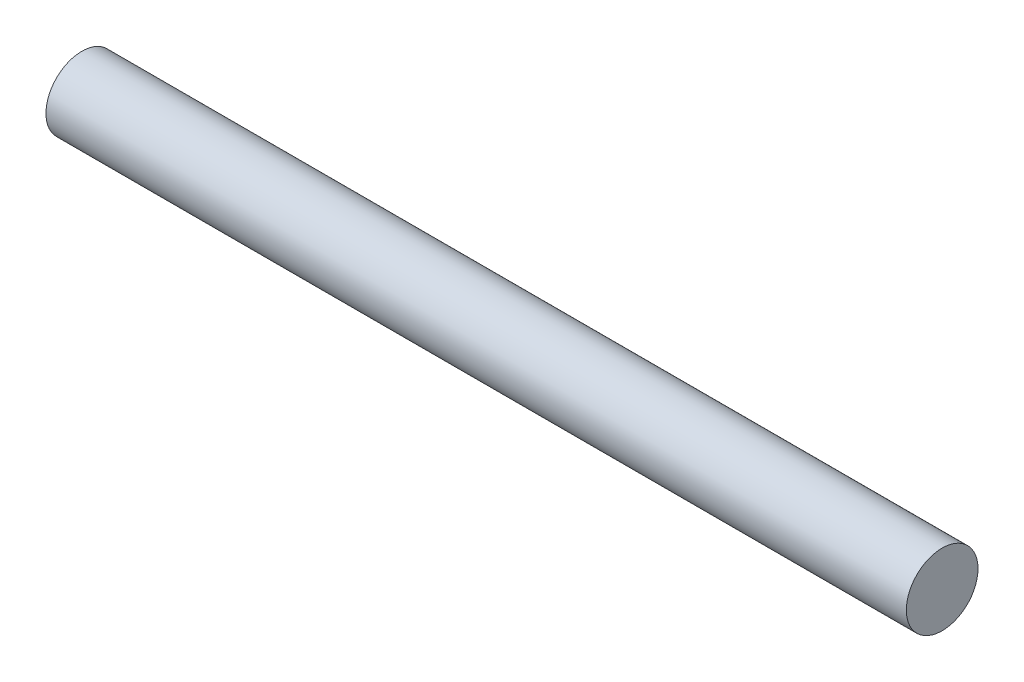
SolidWorks part; units mm, degrees
ref_plane "Front Plane" through (0, 0, 0) normal (0, 0, 1) x (1, 0, 0)
ref_plane "Top Plane" through (0, 0, 0) normal (0, 1, 0) x (1, 0, 0)
ref_plane "Right Plane" through (0, 0, 0) normal (1, 0, 0) x (0, 0, -1)
sketch "Sketch1" plane through (0, 0, 0) normal (1, 0, 0) x (0, 0, -1)
  circle A0 centre (0, 0) radius 4
  dimension "D1" = 8
extrude "Boss-Extrude1" add sketch "Sketch1" along normal blind 96 contours A0
